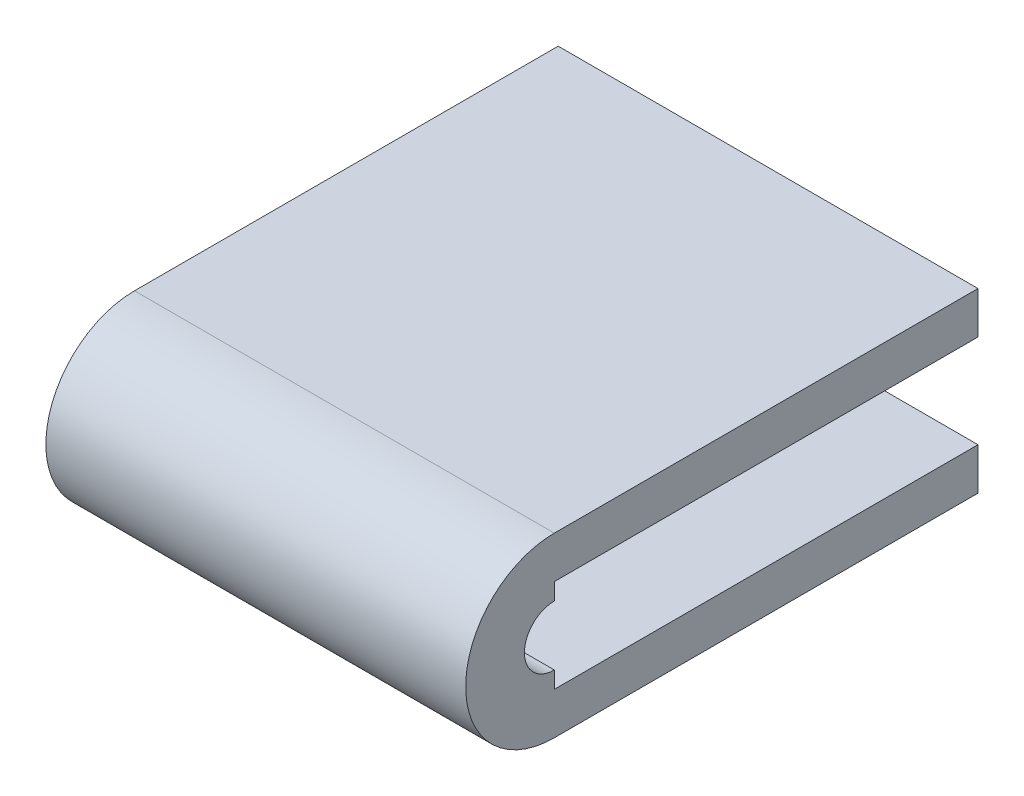
SolidWorks part; units mm, degrees
ref_plane "Front Plane" through (0, 0, 0) normal (0, 0, 1) x (1, 0, 0)
ref_plane "Top Plane" through (0, 0, 0) normal (0, 1, 0) x (1, 0, 0)
ref_plane "Right Plane" through (0, 0, 0) normal (1, 0, 0) x (0, 0, -1)
sketch "Sketch1" plane through (0, 0, 0) normal (1, 0, 0) x (0, 0, -1)
  line L0 (0, 2.032) -> (0, -2.032) construction
  line L1 (0, 6.0325) -> (28.8417, 6.0325)
  line L2 (0, 6.0325) -> (0, 2.032)
  line L3 (0, -6.0325) -> (28.8417, -6.0325)
  line L4 (28.8417, 6.0325) -> (28.8417, 3.175)
  line L5 (0, -2.032) -> (0, -6.0325)
  line L6 (28.8417, 3.175) -> (28.8417, -3.175) construction
  line L7 (0, 3.175) -> (28.8417, 3.175)
  line L8 (0, 3.175) -> (0, -3.175)
  line L9 (0, -3.175) -> (28.8417, -3.175)
  line L10 (28.8417, 3.175) -> (28.8417, -3.175) construction
  line L11 (28.8417, -3.175) -> (28.8417, -6.0325)
  arc A0 (0, 6.0325) -> (0, -6.0325) centre (0, 0) ccw
  arc A1 (0, 2.032) -> (0, -2.032) centre (0, 0) ccw
  arc A2 (0, -2.032) -> (0, 2.032) centre (0, 0) ccw construction
  arc A3 (0, -6.0325) -> (0, 6.0325) centre (0, 0) ccw construction
  point P12 (0, 0)
  point P14 (0, 0)
  dimension "D1" = 12.065
  dimension "D2" = 4.064
  dimension "D3" = 6.35
  dimension "D4" = 28.8417
extrude "Boss-Extrude1" add sketch "Sketch1" along normal blind 28.575 contours L2 L7 L4 L1 | A1 L2 A0 L5 | L11 L9 L5 L3
